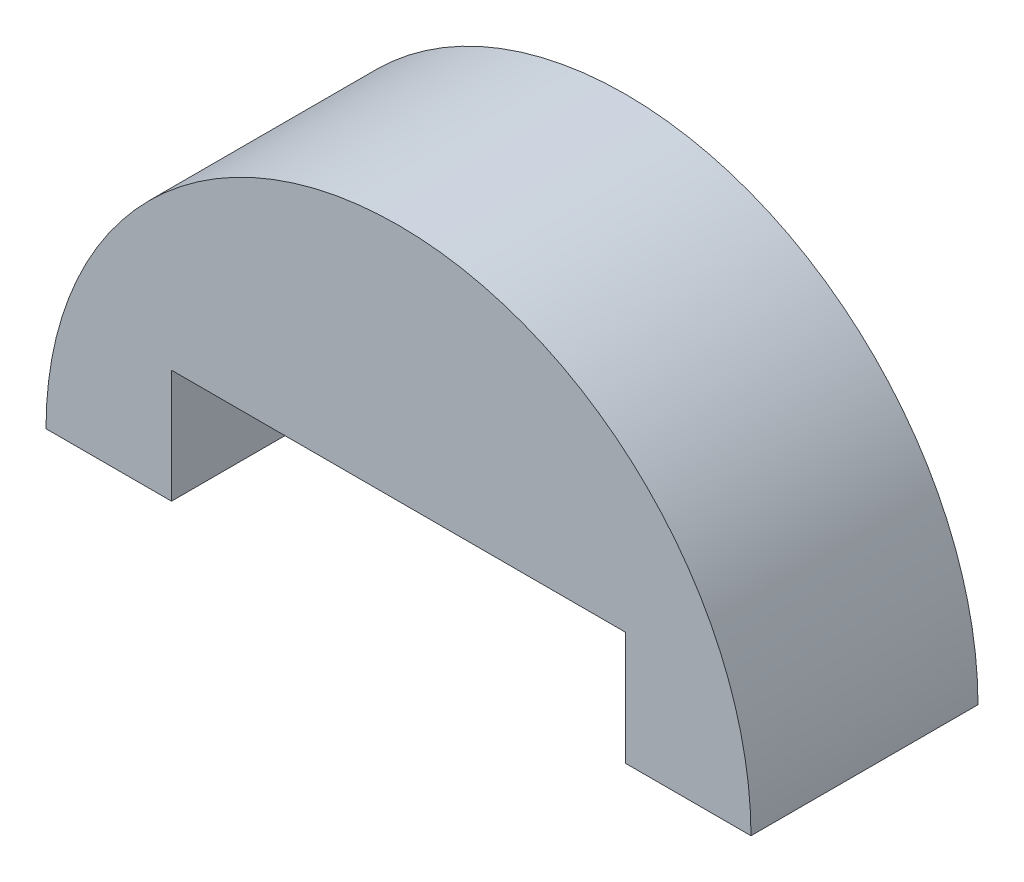
SolidWorks part; units mm, degrees
ref_plane "Front Plane" through (0, 0, 0) normal (0, 0, 1) x (1, 0, 0)
ref_plane "Top Plane" through (0, 0, 0) normal (0, 1, 0) x (1, 0, 0)
ref_plane "Right Plane" through (0, 0, 0) normal (1, 0, 0) x (0, 0, -1)
sketch "Model" plane through (0, 0, 0) normal (0, 0, 1) x (1, 0, 0)
  line L0 (3552.3192, 1325.3809) -> (3555.6363, 1325.3809)
  line L1 (3567.6363, 1325.3809) -> (3570.9534, 1325.3809)
  line L2 (3567.6363, 1328.3809) -> (3567.6363, 1325.3809)
  line L3 (3555.6363, 1328.3809) -> (3555.6363, 1325.3809)
  line L4 (3555.6363, 1328.3809) -> (3567.6363, 1328.3809)
  arc A0 (3570.9534, 1325.3809) -> (3552.3192, 1325.3809) centre (3561.6363, 1325.3809) ccw
extrude "Boss-Extrude1" add sketch "Model" along normal blind 6 contours A0 L0 L3 L4 L2 L1
